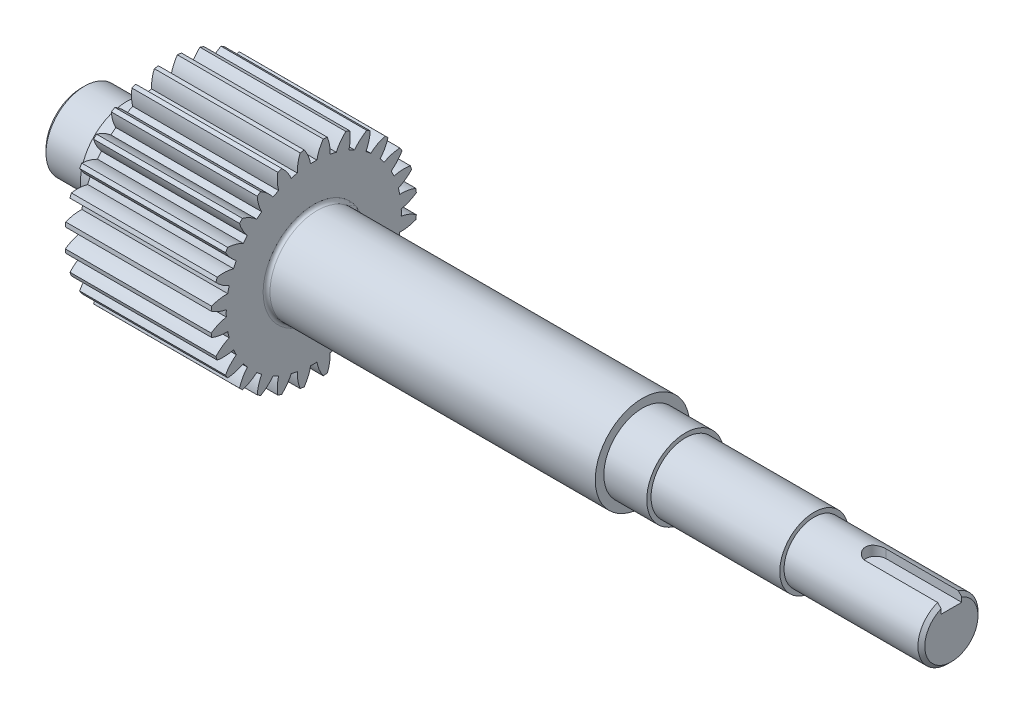
SolidWorks part; units mm, degrees
ref_plane "Plane1" through (0, 0, 0) normal (0, 0, 1) x (1, 0, 0)
ref_plane "Plane2" through (0, 0, 0) normal (0, 1, 0) x (1, 0, 0)
ref_plane "Plane3" through (0, 0, 0) normal (1, 0, 0) x (0, 0, -1)
other "Configuration Table"
sketch "HoldingSke" plane through (0, 0, 0) normal (0, 1, 0) x (1, 0, 0)
  line L0 (0, 0) -> (0.2207, -0.1174)
  line L1 (-15, 0) -> (100, 0) construction
  line L2 (0, 0) -> (-2.1039, 2.3779)
  line L3 (0, 0) -> (-11.863, 4.5341)
  line L4 (0, 0) -> (7.6251, 4.0544)
  line L5 (0, 0) -> (-46.8476, -17.4728)
  line L6 (0, 0) -> (-70.4618, -47.5408)
  line L7 (-2.1039, 2.3779) -> (16.1923, 85.3855)
  line L8 (-76.2, 54.61) -> (-76.1, 54.61)
  line L9 (-71.009, 38.7566) -> (-53.1078, 45.2721)
  line L10 (-76.2, 71.12) -> (104.1128, 71.12)
  line L11 (0, 0) -> (-85, 0)
  line L12 (-76.2, 101.6) -> (-76.073, 101.6)
  line L13 (24.9733, 27.94) -> (52.9518, 28.4284)
  line L14 (24.9733, 27.94) -> (24.9743, 27.94)
  line L15 (24.9733, 27.94) -> (100.4006, 29.5858)
  line L16 (-63.627, -4) -> (-12.827, -4)
  circle A0 centre (0, 0) radius 0.4
  circle A1 centre (0, 0) radius 37.5
  circle A2 centre (0, 0) radius 37.5
  circle A3 centre (0, 0) radius 0.4
  dimension "MHD" = 75
  dimension "Hub_dia" = 75
  dimension "Bore" = 0.8
  dimension "MBD" = 0.8
  dimension "Num_teeth" = 28
  dimension "Pitch" = 0.25
  dimension "Overall_len" = 50
  dimension "Show_teeth" = 28
  dimension "Thickness" = 85
  dimension "OAL" = 85.0001
  dimension "T_dim" = 0.1
  dimension "Ap" = 20
  dimension "H" = 19.05
  dimension "Pitch_radius" = 180.3128
  dimension "Width" = 85
  dimension "Backlash" = 0.127
  dimension "Addendum_fac" = 1
  dimension "Dedendum_fac" = 1.25
  dimension "Clearance_fac" = 0.25
  dimension "Dedendum_add" = 0.001
  dimension "Module" = 4
sketch "BasProSke" plane through (0, 0, 0) normal (0, 1, 0) x (1, 0, 0)
  line L0 (-10, 0) -> (60, 0) construction
  line L1 (0, 0) -> (0, 60)
  line L2 (0, 0) -> (85, 0)
  line L3 (85, 0) -> (85, 60)
  line L4 (85, 60) -> (0, 60)
  dimension "Thickness" = 85
  dimension "Diameter" = 120
revolve "Base-Revolve" add sketch "BasProSke" angle 360 about L0
sketch "TooCutSke" plane through (0, 0, 0) normal (1, 0, 0) x (0, 0, -1)
  line L1 (0, 0) -> (0, 107) construction
  line L2 (0, 0) -> (-3.3621, 55.899) construction
  line L3 (0, 0) -> (-12.523, 111.1446) construction
  line L4 (-3.3621, 55.899) -> (-6.2615, 55.5723) construction
  arc A0 (1.846, 50.9656) -> (-1.846, 50.9656) centre (0, 0) ccw
  arc A1 (5.5418, 59.769) -> (-5.5418, 59.769) centre (0, 0) ccw
  circle A2 centre (0, 0) radius 56 construction
  circle A3 centre (0, 0) radius 52.6228 construction
  arc A4 (-1.846, 50.9656) -> (-5.5418, 59.769) centre (-23.8732, 46.8959) ccw
  arc A5 (5.5418, 59.769) -> (1.846, 50.9656) centre (23.8732, 46.8959) ccw
  dimension "Root_dia" = 101.998
  dimension "Overcut_dia" = 120.0508
  dimension "Pitch_dia" = 112
  dimension "Base_dia" = 105.2456
  dimension "Flank_rad" = 22.4
  dimension "Half_ang" = 6.429
  dimension "Half_CT" = 2.9177
extrude "ToothCut" cut sketch "TooCutSke" along normal through all
fillet "Breaks" [suppressed] radius 0.08
fillet "RootFillets" [suppressed] radius 1.001
pattern_circular "TeethCuts" count 28 every 12.857 about axis through (-10, 0, 0) along (1, 0, 0) of "ToothCut", "RootFillets", "Breaks"
sketch "HubNeaOneSke" plane through (0, 0, 0) normal (-1, 0, 0) x (0, 0, 1)
  circle A0 centre (0, 0) radius 37.5
  dimension "Diameter" = 75
extrude "HubNearOne" [suppressed] add sketch "HubNeaOneSke" along normal blind 38.0001
sketch "HubNeaBotSke" plane through (0, 0, 0) normal (-1, 0, 0) x (0, 0, 1)
  circle A0 centre (0, 0) radius 37.5
  dimension "Diameter" = 75
extrude "HubNearBoth" [suppressed] add sketch "HubNeaBotSke" along normal blind 19
ref_plane "FarPln" through (85, 0, 0) normal (1, 0, 0) x (0, 0, -1)
sketch "HubFarSke" plane through (85, 0, 0) normal (1, 0, 0) x (0, 0, -1)
  circle A0 centre (0, 0) radius 37.5
  dimension "Diameter" = 75
extrude "HubFar" [suppressed] add sketch "HubFarSke" along normal blind 19
sketch "BorSke" plane through (0, 0, 0) normal (1, 0, 0) x (0, 0, -1)
  circle A0 centre (0, 0) radius 0.4
  dimension "Diameter" = 0.8
extrude "Bore" cut sketch "BorSke" along normal mid plane 170.0001
sketch "KeySke" plane through (0, 0, 0) normal (1, 0, 0) x (0, 0, -1)
  line L0 (-0.05, 0) -> (-0.05, 0.5)
  line L1 (-0.05, 0.5) -> (0.05, 0.5)
  line L2 (0.05, 0.5) -> (0.05, 0)
  line L3 (0, 0) -> (0, 34) construction
  line L4 (-0.05, 0) -> (0.05, 0)
  dimension "Offset" = 0.5
  dimension "Width" = 0.1
extrude "Keyway" [suppressed] cut sketch "KeySke" along normal mid plane 170.0001
pattern_circular "Keyway2" [suppressed] count 2 every 90 about axis through (-10, 0, 0) along (1, 0, 0)
sketch "Sketch1" plane through (0, 0, 0) normal (0, 0, 1) x (1, 0, 0)
  line L0 (0, 0) -> (456.5, 0)
  line L1 (0, 1.846) -> (0, -1.846) construction
  line L2 (456.5, 0) -> (456.5, 17.5)
  line L3 (456.5, 17.5) -> (376.5, 17.5)
  line L4 (376.5, 17.5) -> (376.5, 20)
  line L5 (376.5, 20) -> (301.5, 20)
  line L6 (301.5, 20) -> (301.5, 22.5)
  line L7 (301.5, 22.5) -> (276.5, 22.5)
  line L8 (276.5, 22.5) -> (276.5, 27.5)
  line L9 (276.5, 27.5) -> (-23.5, 27.5)
  line L10 (-23.5, 27.5) -> (-23.5, 22.5)
  line L11 (-23.5, 22.5) -> (-50.5, 22.5)
  line L12 (-50.5, 22.5) -> (-50.5, 0)
  line L13 (-50.5, 0) -> (0, 0)
  line L14 (309.8766, 0) -> (-140.423, 0) construction
  line L15 (0, 41.57) -> (0, 33.2198) construction
  dimension "D1" = 45
  dimension "D2" = 55
  dimension "D3" = 35
  dimension "D4" = 40
  dimension "D5" = 45
  dimension "D6" = 80
  dimension "D7" = 75
  dimension "D8" = 25
  dimension "D9" = 191.5
  dimension "D10" = 23.5
  dimension "D11" = 50.5
revolve "Revolve1" add sketch "Sketch1" angle 360 about L14
fillet "Fillet1" radius 2 2 edges at (0, 0, -27.5) (85, 0, 27.5)
chamfer "Chamfer1" distance 2 angle 45 2 edges at (-50.5, 22.5, 0) (456.5, 17.5, 0)
sketch "Sketch2" plane through (0, 0, 0) normal (0, 1, 0) x (1, 0, 0)
  line L0 (412.5, 0) -> (500.5, 0) construction
  line L1 (412.5, 6) -> (500.5, 6)
  line L2 (412.5, -6) -> (500.5, -6)
  line L3 (456.5, -15.5) -> (456.5, 15.5) construction
  arc A0 (412.5, 6) -> (412.5, -6) centre (412.5, 0) ccw
  arc A1 (500.5, -6) -> (500.5, 6) centre (500.5, 0) ccw
  point P3 (456.5, 0)
  point P8 (0, 0)
  dimension "D1" = 6
  dimension "D2" = 88
extrude "Cut-Extrude1" cut sketch "Sketch2" along normal through all from offset 11.5
equation "' \"Module@HoldingSke\" = 6.35"
equation "' \"Num_teeth@HoldingSke\" = 12"
equation "' \"Ap@HoldingSke\" =  20"
equation "' \"Ap@HoldingSke\" = 20"
equation "' \"Width@HoldingSke\" = 0.5 * 25.4"
equation "' \"Hub_dia@HoldingSke\"= 1 * 25.4"
equation "' \"Hub_dia@HoldingSke\" = 1 * 25.4"
equation "' \"Overall_len@HoldingSke\" = 1.0 * 25.4"
equation "' \"Bore@HoldingSke\" = 0.75 * 25.4"
equation "' \"T_dim@HoldingSke\" = 0.1 * 25.4"
equation "' \"Width@KeySke\" = 0.25 * 25.4"
equation "' \"Show_teeth@HoldingSke\" = 13"
equation "' \"Backlash@HoldingSke\" = 0.009 * 25.4"
equation "' \"Addendum_fac@HoldingSke\" = 1.0"
equation "' \"Dedendum_fac@HoldingSke\" = 1.25"
equation "' \"Dedendum_add@HoldingSke\" = 0.00005 * 25.4"
equation "' \"Clearance_fac@HoldingSke\" = 0.25"
equation "\"Pitch@HoldingSke\" = 1 / \"Module@HoldingSke\""
equation "\"Overcut_dia@TooCutSke\" = (\"Num_teeth@HoldingSke\" + 2 * \"Addendum_fac@HoldingSke\") / \"Pitch@HoldingSke\" + 0.002 * 25.4"
equation "\"Pitch_dia@TooCutSke\" = \"Num_teeth@HoldingSke\" / \"Pitch@HoldingSke\""
equation "\"Base_dia@TooCutSke\" = \"Num_teeth@HoldingSke\" / \"Pitch@HoldingSke\" * cos((\"Ap@HoldingSke\"  * 3.14159265 / 180))"
equation "\"Root_dia@TooCutSke\" = (\"Num_teeth@HoldingSke\" + 2) / \"Pitch@HoldingSke\" - 2 * (\"Addendum_fac@HoldingSke\" + \"Dedendum_fac@HoldingSke\") / \"Pitch@HoldingSke\" - \"Dedendum_add@HoldingSke\" * 2"
equation "\"Half_ang@TooCutSke\" = 180 / \"Num_teeth@HoldingSke\""
equation "\"Half_CT@TooCutSke\" = \"Num_teeth@HoldingSke\" / \"Pitch@HoldingSke\" * sin((3.14159265 / 2 / \"Num_teeth@HoldingSke\")) / 2 - 7 * \"Backlash@HoldingSke\" / 4"
equation "\"Flank_rad@TooCutSke\" = \"Num_teeth@HoldingSke\" / \"Pitch@HoldingSke\" / 5"
equation "\"Radius@RootFillets\" = \"Clearance_fac@HoldingSke\" / \"Pitch@HoldingSke\" + \"Dedendum_add@HoldingSke\""
equation "\"Break_rad@Breaks\" = 0.02 / \"Pitch@HoldingSke\""
equation "\"Thickness@HoldingSke\" = \"Width@HoldingSke\""
equation "\"OAL@HoldingSke\" = \"Thickness@HoldingSke\""
equation "\"MHD@HoldingSke\" = (\"Num_teeth@HoldingSke\" + 2) / \"Pitch@HoldingSke\" - 2 * (\"Addendum_fac@HoldingSke\" + \"Dedendum_fac@HoldingSke\")  / \"Pitch@HoldingSke\" - \"Dedendum_add@HoldingSke\" * 2"
equation "\"MBD@HoldingSke\" = (\"Num_teeth@HoldingSke\" + 2) / \"Pitch@HoldingSke\" - 2 * (\"Addendum_fac@HoldingSke\" + \"Dedendum_fac@HoldingSke\")  / \"Pitch@HoldingSke\" - \"Dedendum_add@HoldingSke\" * 2 - 0.002 * 25.4"
equation "\"MHD@HoldingSke\" = ((sgn( \"MHD@HoldingSke\" - \"Hub_dia@HoldingSke\" )-1)*( \"MHD@HoldingSke\" - \"Hub_dia@HoldingSke\" ))/-2+ \"Hub_dia@HoldingSke\""
equation "\"MBD@HoldingSke\" = ((sgn( \"MBD@HoldingSke\" - \"Bore@HoldingSke\" )-1)*( \"MBD@HoldingSke\" - \"Bore@HoldingSke\" ))/-2+ \"Bore@HoldingSke\""
equation "\"OAL@HoldingSke\" = ((sgn( \"OAL@HoldingSke\" - \"Overall_len@HoldingSke\" )+1)*( \"OAL@HoldingSke\" - \"Overall_len@HoldingSke\" ))/2 + \"Overall_len@HoldingSke\" + 0.000002 * 25.4"
equation "\"Num_teeth@TeethCuts\" = int( \"Show_teeth@HoldingSke\" ) + 1"
equation "\"Num_teeth@TeethCuts\" = ((sgn( \"Num_teeth@TeethCuts\" - \"Num_teeth@HoldingSke\" )-1)*( \"Num_teeth@TeethCuts\" - \"Num_teeth@HoldingSke\" ))/-2+ \"Num_teeth@HoldingSke\""
equation "\"Num_teeth@TeethCuts\" = ((sgn( \"Num_teeth@TeethCuts\" - 2.0)+1)*( \"Num_teeth@TeethCuts\" - 2.0))/2 +2.0"
equation "\"Angle@TeethCuts\" = 360.0 / \"Num_teeth@HoldingSke\""
equation "\"Diameter@BasProSke\" = (\"Num_teeth@HoldingSke\" + 2 * \"Addendum_fac@HoldingSke\") / \"Pitch@HoldingSke\""
equation "\"Thickness@BasProSke\"  = \"Thickness@HoldingSke\""
equation "' \"Fillet_rad@BasProSke\" =  \"Thickness@HoldingSke\" * 0.05"
equation "' \"Fillet_rad@BasProSke\" = \"Thickness@HoldingSke\" * 0.05"
equation "\"MHD@HoldingSke\" = ((sgn( \"MHD@HoldingSke\" - \"Root_dia@TooCutSke\" )-1)*( \"MHD@HoldingSke\" - \"Root_dia@TooCutSke\" ))/-2+ \"Root_dia@TooCutSke\""
equation "\"Diameter@HubNeaOneSke\" = \"MHD@HoldingSke\""
equation "\"Length@HubNearOne\" = \"OAL@HoldingSke\" - \"Thickness@BasProSke\""
equation "\"Diameter@HubNeaBotSke\" = \"MHD@HoldingSke\""
equation "\"Length@HubNearBoth\" = ( \"OAL@HoldingSke\" - \"Thickness@BasProSke\" ) / 2.0"
equation "\"Thickness@FarPln\" = \"Thickness@BasProSke\""
equation "\"Diameter@HubFarSke\" = \"MHD@HoldingSke\""
equation "\"Length@HubFar\" = ( \"OAL@HoldingSke\" - \"Thickness@BasProSke\" ) / 2.0"
equation "\"Diameter@BorSke\" = \"MBD@HoldingSke\""
equation "\"D1@Bore\" = \"OAL@HoldingSke\" * 2.0"
equation "\"D1@Keyway\" = \"OAL@HoldingSke\" * 2.0"
equation "\"Offset@KeySke\" = \"T_dim@HoldingSke\" + \"MBD@HoldingSke\" / 2.0"
equation "\"D2@Sketch2\"=100-12"
